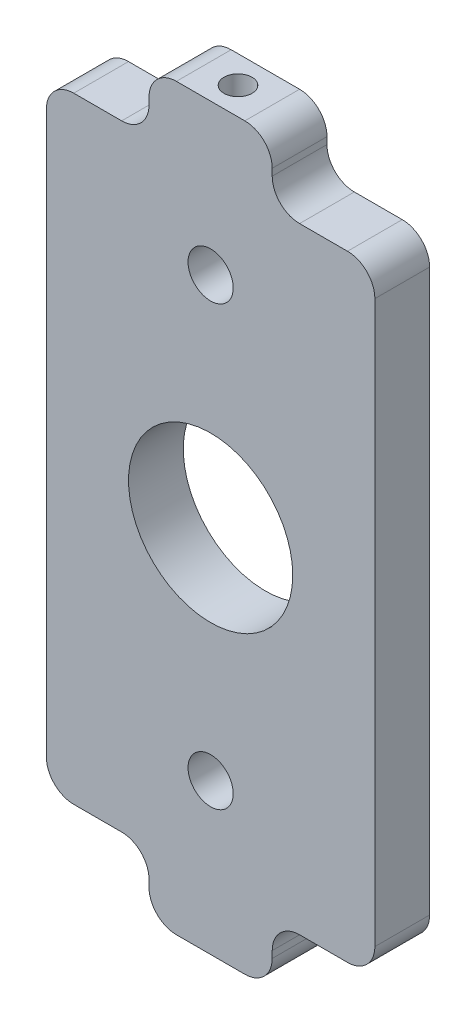
SolidWorks part; units mm, degrees
ref_plane "前视基准面" through (0, 0, 0) normal (0, 0, 1) x (1, 0, 0)
ref_plane "上视基准面" through (0, 0, 0) normal (0, 1, 0) x (1, 0, 0)
ref_plane "右视基准面" through (0, 0, 0) normal (1, 0, 0) x (0, 0, -1)
sketch "草图3" plane through (0, 0, 0) normal (0, 0, 1) x (1, 0, 0)
  line L13 (-2.5, -27) -> (2.5, -27)
  line L15 (4.5, -25) -> (4.5, -24.5)
  line L17 (6.5, -22.5) -> (10, -22.5)
  line L19 (12, -20.5) -> (12, 20.5)
  line L21 (10, 22.5) -> (4.5, 22.5)
  line L23 (4.5, 22.5) -> (4.5, 25)
  line L25 (2.5, 27) -> (-2.5, 27)
  line L27 (-4.5, 25) -> (-4.5, 22.5)
  line L29 (-4.5, 22.5) -> (-10, 22.5)
  line L31 (-12, 20.5) -> (-12, -20.5)
  line L33 (-10, -22.5) -> (-6.5, -22.5)
  line L35 (-4.5, -24.5) -> (-4.5, -25)
  arc A2 (2.5, -27) -> (4.5, -25) centre (2.5, -25) ccw
  circle A4 centre (0, 0) radius 6
  arc A19 (6.5, -22.5) -> (4.5, -24.5) centre (6.5, -24.5) ccw
  arc A21 (10, -22.5) -> (12, -20.5) centre (10, -20.5) ccw
  arc A23 (12, 20.5) -> (10, 22.5) centre (10, 20.5) ccw
  arc A25 (4.5, 25) -> (2.5, 27) centre (2.5, 25) ccw
  arc A27 (-2.5, 27) -> (-4.5, 25) centre (-2.5, 25) ccw
  arc A29 (-10, 22.5) -> (-12, 20.5) centre (-10, 20.5) ccw
  arc A31 (-12, -20.5) -> (-10, -22.5) centre (-10, -20.5) ccw
  arc A33 (-4.5, -24.5) -> (-6.5, -22.5) centre (-6.5, -24.5) ccw
  arc A35 (-4.5, -25) -> (-2.5, -27) centre (-2.5, -25) ccw
extrude "凸台-拉伸1" add sketch "草图3" along normal blind 4
ref_plane "基准面1" through (0, 27, 0) normal (0, 1, 0) x (1, 0, 0)
sketch "草图4" plane through (0, 27, 0) normal (0, 1, 0) x (1, 0, 0)
  line L0 (-2.5, -2) -> (2.5, -2) construction
  line L1 (0, 0) -> (0, -4) construction
hole_wizard "M2.5 螺纹孔1" positions "草图5" profile "草图6" tap size "M2.5" standard "GB"
sketch "草图5" plane through (0, 27, 0) normal (0, 1, 0) x (1, 0, 0)
  line L0 (-2.5, -2) -> (2.5, -2) construction
  point P0 (0, -2)
sketch "草图6" plane through (0, 27, 2) normal (1, 0, 0) x (0, 0, 1)
  line L0 (0, 0) -> (0, 7.8659)
  line L1 (0, 7.8659) -> (1.025, 7.25)
  line L2 (1.025, 7.25) -> (1.025, 0)
  line L5 (1.025, 0) -> (0, 0)
  line L10 (0, 7.8659) -> (-1.025, 7.25) construction
  line L11 (0, -6.35) -> (0, 107.95) construction
  dimension "螺纹孔钻头直径" = 2.05
  dimension "螺纹孔钻头深度" = 7.25
  dimension "导头角度" = 118
cosmetic thread "孔螺蚊线1" parameters "D1"=5, "D2"=2.5
mirror "镜向1" about plane through (0, 0, 0) normal (0, 1, 0) of "M2.5 螺纹孔1"
fillet "圆角1" radius 2 2 edges at (4.5, 22.5, 2) (-4.5, 22.5, 2)
sketch "草图7" plane through (0, 0, 0) normal (0, 0, 1) x (1, 0, 0)
  line L0 (0, 0) -> (0, 27) construction
  line L1 (0, 0) -> (0, -27) construction
  line L2 (0, -6) -> (0, -16)
  line L4 (0, 6) -> (0, 16)
  point P9 (0, 0)
hole_wizard "M4 螺纹孔2" positions "草图10" profile "草图11" tap size "M4" standard "GB"
sketch "草图10" plane through (0, 0, 0) normal (0, 0, -1) x (-1, 0, 0)
  point P0 (0, 16)
  point P3 (0, -16)
sketch "草图11" plane through (0, 16, 0) normal (1, 0, 0) x (0, 1, 0)
  line L0 (0, 0) -> (0, 12.4914)
  line L1 (0, 12.4914) -> (1.65, 11.5)
  line L2 (1.65, 11.5) -> (1.65, 0)
  line L5 (1.65, 0) -> (0, 0)
  line L10 (0, 12.4914) -> (-1.65, 11.5) construction
  line L11 (0, -6.35) -> (0, 107.95) construction
  dimension "螺纹孔钻头直径" = 3.3
  dimension "螺纹孔钻头深度" = 11.5
  dimension "导头角度" = 118
cosmetic thread "孔螺蚊线4" parameters "D1"=4, "D2"=4
cosmetic thread "孔螺蚊线5" parameters "D1"=4, "D2"=4
